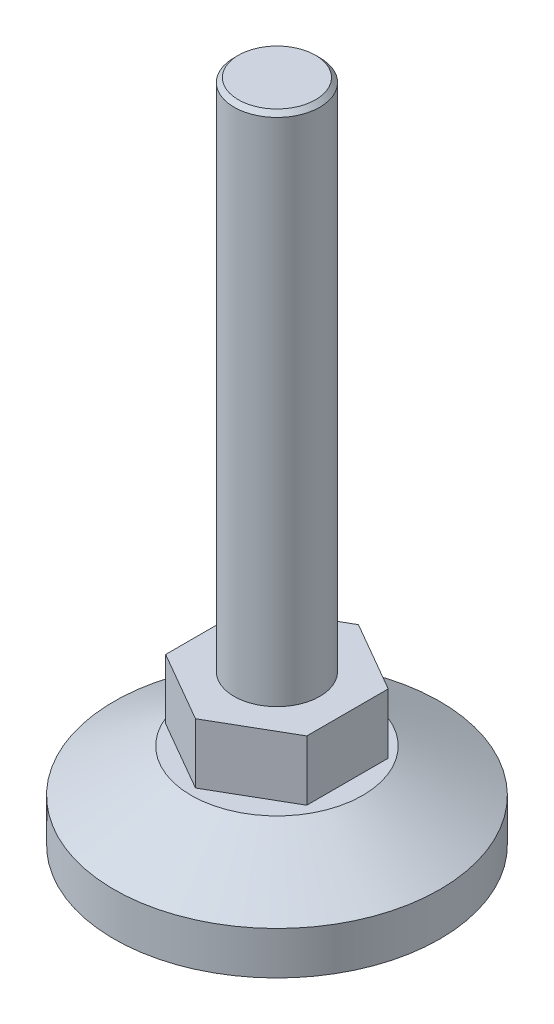
SolidWorks part; units mm, degrees
ref_plane "Спереди" through (0, 0, 0) normal (0, 0, 1) x (1, 0, 0)
ref_plane "Сверху" through (0, 0, 0) normal (0, 1, 0) x (1, 0, 0)
ref_plane "Справа" through (0, 0, 0) normal (1, 0, 0) x (0, 0, -1)
sketch "Эскиз1" plane through (0, 0, 0) normal (0, 0, 1) x (1, 0, 0)
  line L0 (0, 0) -> (0, 77.5) construction
  line L1 (0, 77.5) -> (-5, 77.5)
  line L2 (-5, 77.5) -> (-5, 17.5)
  line L3 (-5, 17.5) -> (-9.5, 17.5)
  line L4 (-9.5, 17.5) -> (-9.5, 10.5)
  line L5 (-9.5, 10.5) -> (-5, 10.5)
  line L6 (-5, 10.5) -> (-5, 10)
  line L7 (-5, 10) -> (-10, 10)
  line L8 (-10, 10) -> (-19, 5)
  line L9 (-19, 5) -> (-19, 0)
  line L10 (-19, 0) -> (-5, 0)
  line L11 (0, 7) -> (0, 77.5)
  line L12 (0, 7) -> (-5, 7)
  line L13 (-5, 7) -> (-5, 0)
  line L14 (-5, 0) -> (0, 0) construction
  point P3 (-4.0122, 0)
  point P16 (0, 7)
  dimension "D1" = 19
  dimension "D2" = 5
  dimension "D3" = 10
  dimension "D4" = 10
  dimension "D5" = 9.5
  dimension "D6" = 0.5
  dimension "D7" = 7
  dimension "D8" = 5
  dimension "D9" = 5
  dimension "D10" = 60
  dimension "D11" = 5
  dimension "D12" = 7
revolve "Повернуть1" add sketch "Эскиз1" angle 360 about L0
cosmetic thread "Условное изображение резьбы1" parameters "D2"=8.344
chamfer "Фаска1" distance 0.5 angle 45 1 edges at (5, 77.5, 0)
sketch "Эскиз2" plane through (0, 17.5, 0) normal (0, 1, 0) x (1, 0, 0)
  line L1 (0, 9.5) -> (-8.2272, 4.75)
  line L2 (-8.2272, 4.75) -> (-8.2272, -4.75)
  line L3 (-8.2272, -4.75) -> (0, -9.5)
  line L4 (0, -9.5) -> (8.2272, -4.75)
  line L5 (8.2272, -4.75) -> (8.2272, 4.75)
  line L6 (8.2272, 4.75) -> (0, 9.5)
  circle A0 centre (0, 0) radius 12.1398
  circle A1 centre (0, 0) radius 8.2272 construction
  circle A2 centre (0, 0) radius 9.5 construction
  point P3 (0, 9.5)
extrude "Вырез-Вытянуть1" cut sketch "Эскиз2" against normal up to next
